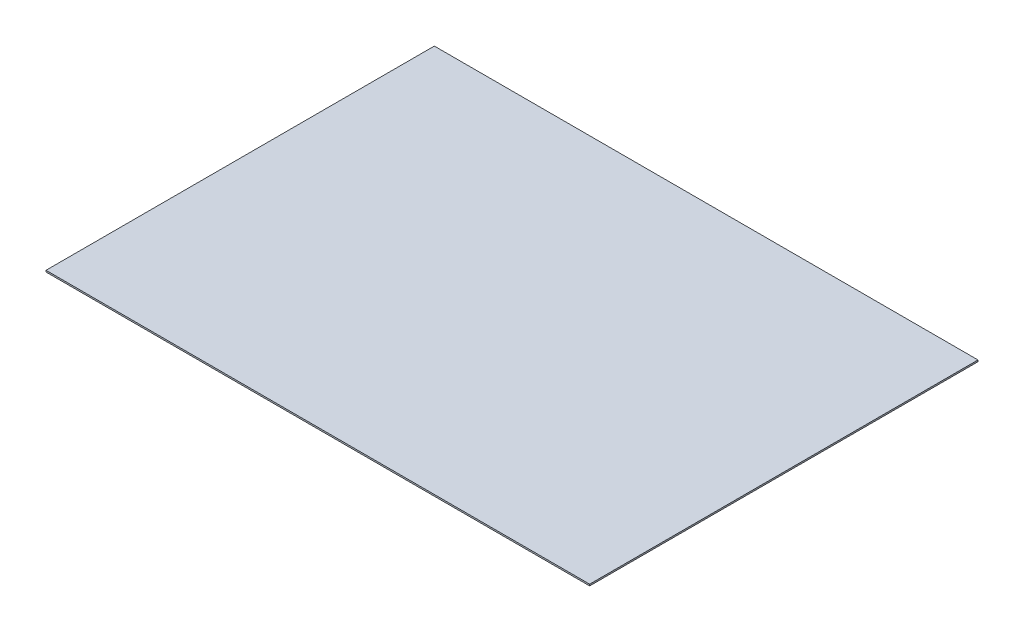
SolidWorks part; units mm, degrees
ref_plane "Front Plane" through (0, 0, 0) normal (0, 0, 1) x (1, 0, 0)
ref_plane "Top Plane" through (0, 0, 0) normal (0, 1, 0) x (1, 0, 0)
ref_plane "Right Plane" through (0, 0, 0) normal (1, 0, 0) x (0, 0, -1)
sketch "Sketch1" plane through (0, 0, 0) normal (0, 1, 0) x (1, 0, 0)
  line L1 (350, -250) -> (-350, -250)
  line L2 (350, -250) -> (350, 250)
  line L3 (350, 250) -> (-350, 250)
  line L4 (-350, -250) -> (-350, 250)
  line L5 (350, -250) -> (-350, 250) construction
  line L6 (350, 250) -> (-350, -250) construction
  point P0 (0, 0)
  dimension "D1" = 500
  dimension "D2" = 700
extrude "Boss-Extrude1" add sketch "Sketch1" along normal blind 2
